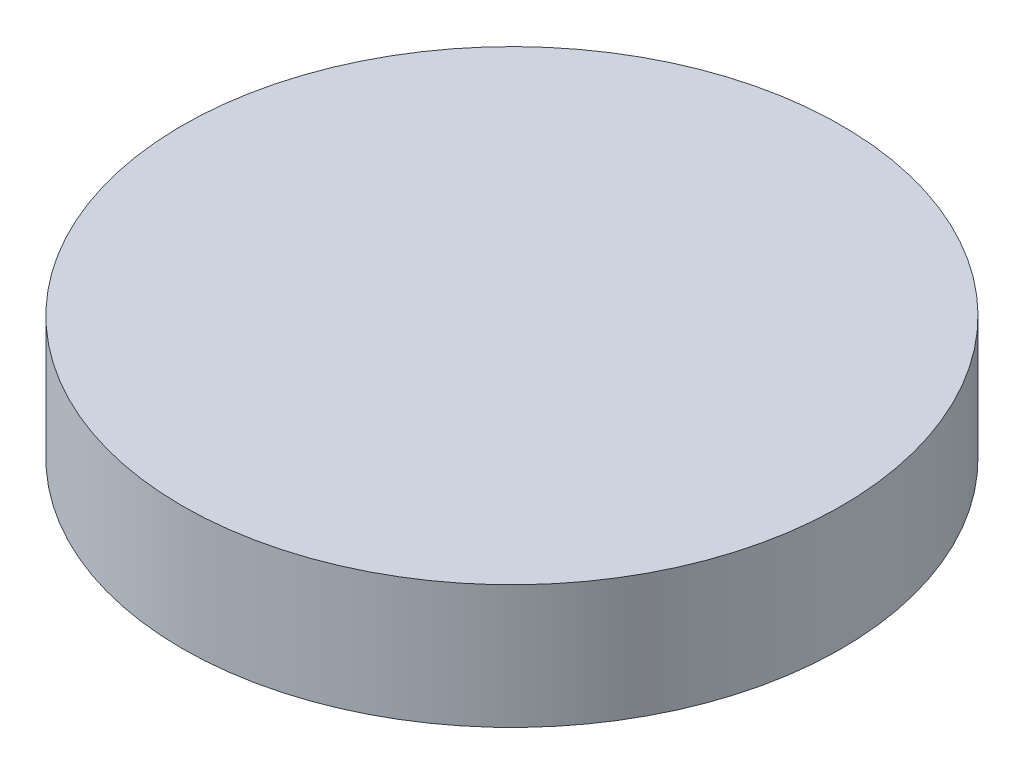
SolidWorks part; units mm, degrees
ref_plane "前视基准面" through (0, 0, 0) normal (0, 0, 1) x (1, 0, 0)
ref_plane "上视基准面" through (0, 0, 0) normal (0, 1, 0) x (1, 0, 0)
ref_plane "右视基准面" through (0, 0, 0) normal (1, 0, 0) x (0, 0, -1)
sketch "草图1" plane through (0, 0, 0) normal (0, 1, 0) x (1, 0, 0)
  circle A0 centre (0, 0) radius 101.6
  dimension "D1" = 203.2
extrude "凸台-拉伸1" add sketch "草图1" along normal blind 38.1
